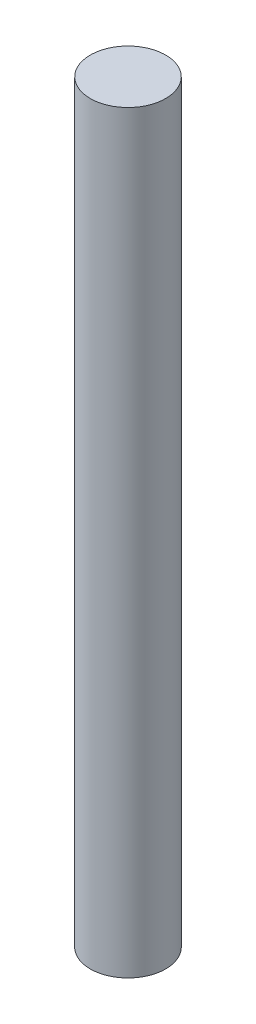
SolidWorks part; units mm, degrees
ref_plane "Front Plane" through (0, 0, 0) normal (0, 0, 1) x (1, 0, 0)
ref_plane "Top Plane" through (0, 0, 0) normal (0, 1, 0) x (1, 0, 0)
ref_plane "Right Plane" through (0, 0, 0) normal (1, 0, 0) x (0, 0, -1)
sketch "Sketch1" plane through (0, 0, 0) normal (0, 1, 0) x (1, 0, 0)
  circle A0 centre (0, 0) radius 2.286
extrude "Boss-Extrude1" add sketch "Sketch1" along normal blind 45.72
equation "\"beaconBoxRodLength\"=1.8"
equation "\"rodDiameter\"=.18"
equation "\"D1@Boss-Extrude1\" = \"beaconBoxRodLength\""
